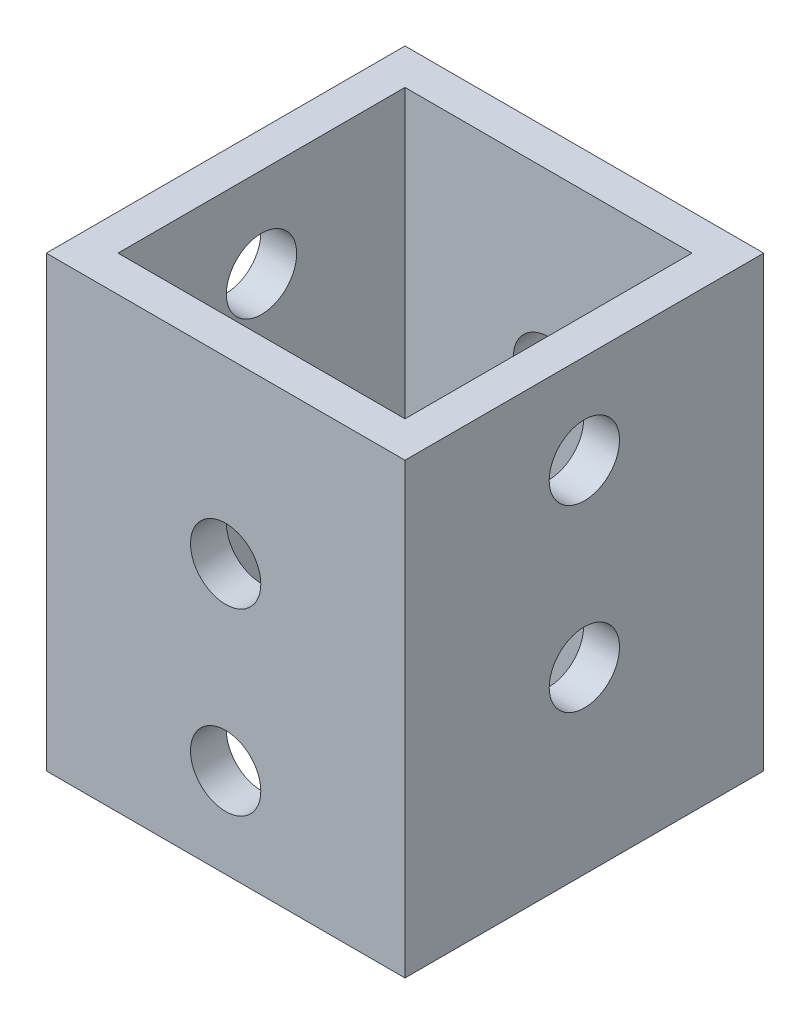
SolidWorks part; units mm, degrees
ref_plane "Front Plane" through (0, 0, 0) normal (0, 0, 1) x (1, 0, 0)
ref_plane "Top Plane" through (0, 0, 0) normal (0, 1, 0) x (1, 0, 0)
ref_plane "Right Plane" through (0, 0, 0) normal (1, 0, 0) x (0, 0, -1)
sketch "Sketch1" plane through (0, 0, 0) normal (0, 1, 0) x (1, 0, 0)
  line L1 (0, 0) -> (25.4, 0)
  line L2 (0, 0) -> (0, 25.4)
  line L3 (0, 25.4) -> (25.4, 25.4)
  line L4 (25.4, 0) -> (25.4, 25.4)
  dimension "D1" = 25.4
  dimension "D2" = 25.4
extrude "Extrude-Thin1" add sketch "Sketch1" along normal blind 31.75 thin thin type one direction reverse wall 2.54
sketch "Sketch2" plane through (0, 0, 0) normal (0, 0, 1) x (1, 0, 0)
  circle A0 centre (12.7, 19.05) radius 2.4892 construction
  circle A1 centre (12.7, 6.35) radius 2.4892 construction
  circle A2 centre (12.7, 19.05) radius 2.4892
  circle A3 centre (12.7, 6.35) radius 2.4892
extrude "Cut-Extrude1" cut sketch "Sketch2" against normal through all
sketch "Sketch3" plane through (0, 0, 0) normal (-1, 0, 0) x (0, 0, 1)
  circle A0 centre (-12.7, 25.4) radius 2.4892 construction
  circle A1 centre (-12.7, 12.7) radius 2.4892 construction
  circle A2 centre (-12.7, 25.4) radius 2.4892
  circle A3 centre (-12.7, 12.7) radius 2.4892
extrude "Cut-Extrude2" cut sketch "Sketch3" against normal through all
